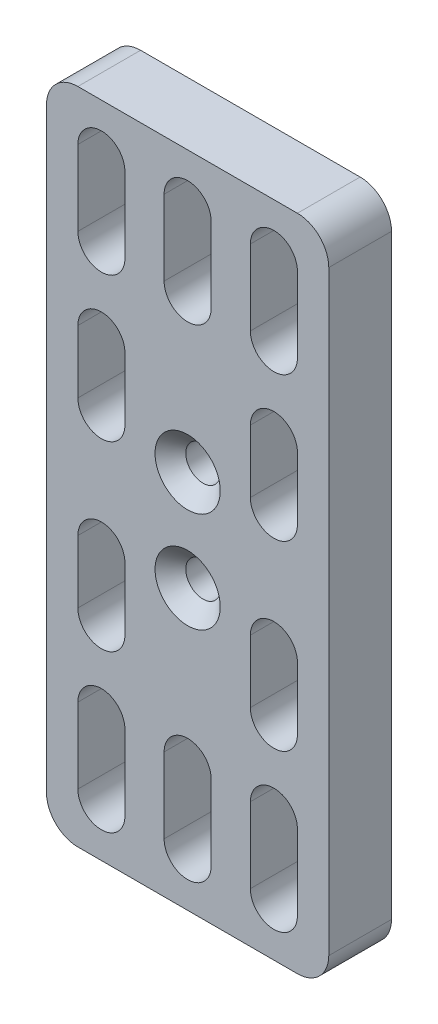
SolidWorks part; units mm, degrees
ref_plane "Front Plane" through (0, 0, 0) normal (0, 0, 1) x (1, 0, 0)
ref_plane "Top Plane" through (0, 0, 0) normal (0, 1, 0) x (1, 0, 0)
ref_plane "Right Plane" through (0, 0, 0) normal (1, 0, 0) x (0, 0, -1)
sketch "Sketch1" plane through (0, 0, 0) normal (0, 0, 1) x (1, 0, 0)
  line L1 (0, 0) -> (45, 0)
  line L2 (0, 0) -> (0, 105)
  line L3 (0, 105) -> (45, 105)
  line L4 (45, 0) -> (45, 105)
  dimension "D1" = 105
  dimension "D2" = 45
extrude "Boss-Extrude1" add sketch "Sketch1" along normal blind 10
sketch "Sketch2" plane through (0, 0, 10) normal (0, 0, 1) x (1, 0, 0)
  line L0 (8.75, 20) -> (8.75, 8) construction
  line L1 (12.5, 20) -> (12.5, 8)
  line L2 (5, 20) -> (5, 8)
  line L3 (0, 0) -> (45, 0) construction
  line L4 (8.75, 72) -> (8.75, 62) construction
  line L5 (12.5, 72) -> (12.5, 62)
  line L6 (5, 72) -> (5, 62)
  line L7 (36.25, 20) -> (36.25, 8) construction
  line L8 (32.5, 20) -> (32.5, 8)
  line L9 (40, 20) -> (40, 8)
  line L10 (36.25, 72) -> (36.25, 62) construction
  line L11 (0, 105) -> (0, 0) construction
  line L12 (0, 52.5) -> (45, 52.5) construction
  line L13 (32.5, 72) -> (32.5, 62)
  line L14 (45, 0) -> (45, 105) construction
  line L15 (40, 72) -> (40, 62)
  line L16 (36.25, 85) -> (36.25, 97) construction
  line L17 (32.5, 85) -> (32.5, 97)
  line L18 (40, 85) -> (40, 97)
  line L19 (36.25, 33) -> (36.25, 43) construction
  line L20 (32.5, 33) -> (32.5, 43)
  line L21 (8.75, 85) -> (8.75, 97) construction
  line L22 (12.5, 85) -> (12.5, 97)
  line L23 (5, 85) -> (5, 97)
  line L24 (22.5, 105) -> (22.5, 0) construction
  line L25 (45, 105) -> (0, 105) construction
  line L26 (40, 33) -> (40, 43)
  line L27 (22.5, 85) -> (22.5, 97) construction
  line L28 (26.25, 85) -> (26.25, 97)
  line L29 (18.75, 85) -> (18.75, 97)
  line L30 (22.5, 20) -> (22.5, 8) construction
  line L31 (26.25, 20) -> (26.25, 8)
  line L32 (18.75, 20) -> (18.75, 8)
  line L33 (8.75, 33) -> (8.75, 43) construction
  line L34 (12.5, 33) -> (12.5, 43)
  line L35 (5, 33) -> (5, 43)
  arc A0 (12.5, 20) -> (5, 20) centre (8.75, 20) ccw
  arc A1 (5, 8) -> (12.5, 8) centre (8.75, 8) ccw
  arc A2 (12.5, 72) -> (5, 72) centre (8.75, 72) ccw
  arc A3 (5, 62) -> (12.5, 62) centre (8.75, 62) ccw
  arc A4 (32.5, 20) -> (40, 20) centre (36.25, 20) cw
  arc A5 (40, 8) -> (32.5, 8) centre (36.25, 8) cw
  arc A6 (32.5, 72) -> (40, 72) centre (36.25, 72) cw
  arc A7 (40, 62) -> (32.5, 62) centre (36.25, 62) cw
  arc A8 (32.5, 85) -> (40, 85) centre (36.25, 85) ccw
  arc A9 (40, 97) -> (32.5, 97) centre (36.25, 97) ccw
  arc A10 (12.5, 85) -> (5, 85) centre (8.75, 85) cw
  arc A11 (5, 97) -> (12.5, 97) centre (8.75, 97) cw
  arc A12 (32.5, 33) -> (40, 33) centre (36.25, 33) ccw
  arc A13 (40, 43) -> (32.5, 43) centre (36.25, 43) ccw
  arc A14 (26.25, 85) -> (18.75, 85) centre (22.5, 85) cw
  arc A15 (18.75, 97) -> (26.25, 97) centre (22.5, 97) cw
  arc A16 (26.25, 20) -> (18.75, 20) centre (22.5, 20) ccw
  arc A17 (18.75, 8) -> (26.25, 8) centre (22.5, 8) ccw
  arc A18 (12.5, 33) -> (5, 33) centre (8.75, 33) cw
  arc A19 (5, 43) -> (12.5, 43) centre (8.75, 43) cw
  point P2 (8.75, 14)
  point P14 (8.75, 67)
  point P21 (36.25, 14)
  point P31 (36.25, 67)
  point P38 (36.25, 91)
  point P45 (8.75, 91)
  point P56 (36.25, 38)
  point P63 (22.5, 91)
  point P71 (22.5, 14)
  point P77 (8.75, 38)
  dimension "D1" = 8
  dimension "D4" = 5
  dimension "D5" = 7.5
fillet "Fillet1" radius 5 4 edges at (45, 0, 5) (0, 0, 5) (0, 105, 5) (45, 105, 5)
extrude "Cut-Extrude1" cut sketch "Sketch2" against normal blind 10
sketch "Sketch3" plane through (0, 0, 10) normal (0, 0, 1) x (1, 0, 0)
  line L0 (22.5, 105) -> (22.5, 0) construction
  line L1 (40, 105) -> (5, 105) construction
  line L2 (5, 0) -> (40, 0) construction
  line L3 (0, 52.5) -> (45, 52.5) construction
  line L4 (0, 100) -> (0, 5) construction
  line L5 (45, 5) -> (45, 100) construction
  point P0 (22.5, 60.5)
  point P1 (22.5, 44.5)
  dimension "D1" = 16
hole_wizard "CSK for M5 Countersunk Flat Head1" positions "Sketch4" profile "Sketch5" countersink size "M5" standard "BSI"
sketch "Sketch4" plane through (0, 0, 10) normal (0, 0, 1) x (1, 0, 0)
  point P0 (22.5, 60.5)
  point P3 (22.5, 44.5)
sketch "Sketch5" plane through (22.5, 60.5, 10) normal (1, 0, 0) x (0, -1, 0)
  line L0 (0, 0) -> (0, 31.6524)
  line L1 (0, 31.6524) -> (2.75, 30)
  line L2 (2.75, 30) -> (2.75, 2.45)
  line L3 (2.75, 2.45) -> (5.2, 0)
  line L5 (5.2, 0) -> (0, 0)
  line L6 (-2.75, 2.45) -> (-5.2, 0) construction
  line L10 (0, 31.6524) -> (-2.75, 30) construction
  line L11 (0, -6.35) -> (0, 107.95) construction
  dimension "Hole Dia." = 5.5
  dimension "Hole Depth" = 30
  dimension "Near C'Sink Dia." = 10.4
  dimension "Near C'Sink Angle" = 90
  dimension "Drill Angle" = 118
